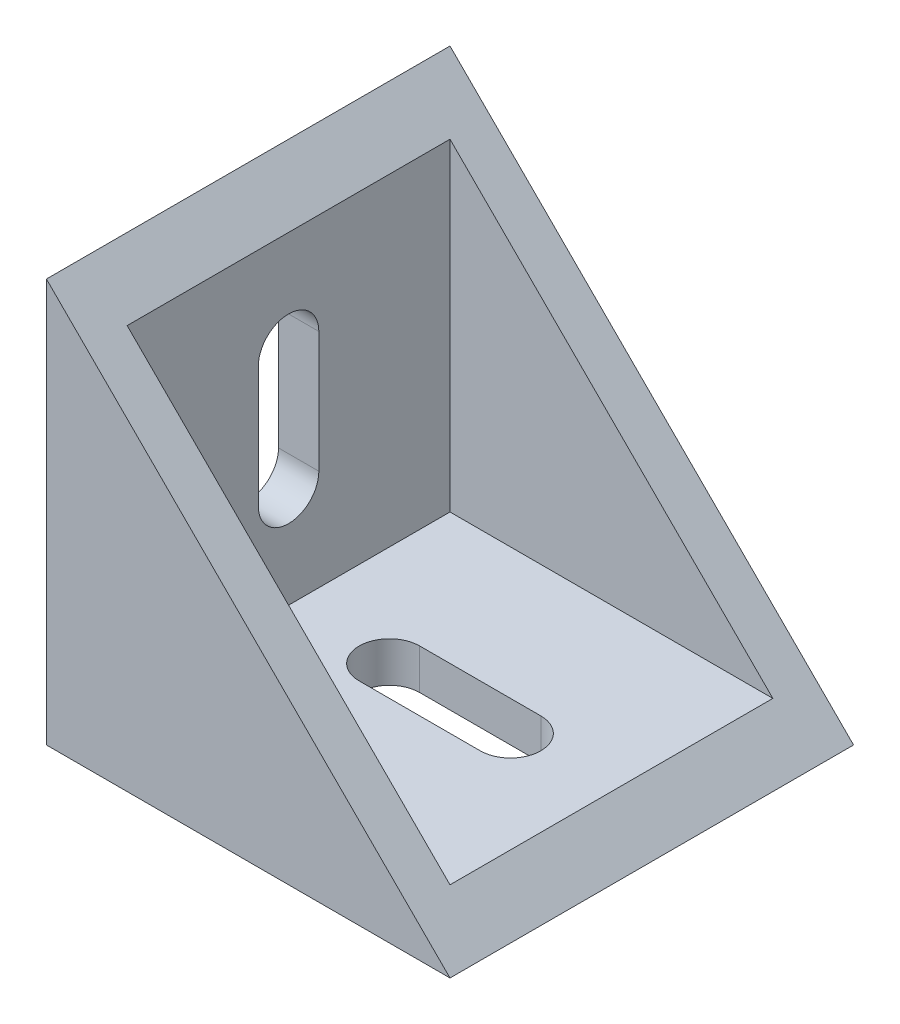
SolidWorks part; units mm, degrees
ref_plane "Front Plane" through (0, 0, 0) normal (0, 0, 1) x (1, 0, 0)
ref_plane "Top Plane" through (0, 0, 0) normal (0, 1, 0) x (1, 0, 0)
ref_plane "Right Plane" through (0, 0, 0) normal (1, 0, 0) x (0, 0, -1)
sketch "Sketch1" plane through (0, 0, 0) normal (0, 0, 1) x (1, 0, 0)
  line L0 (-10, 10) -> (10, -10)
  line L1 (-10, -10) -> (10, -10)
  line L2 (-10, -10) -> (-10, 10)
  line L5 (-10, -10) -> (0, 0) construction
  line L6 (-10, 10) -> (10, -10) construction
  point P0 (0, 0)
  dimension "D1" = 20
extrude "Boss-Extrude1" add sketch "Sketch1" along normal blind 20
shell "Shell1" thickness 2
sketch "Sketch2" plane through (-8, 0, 0) normal (1, 0, 0) x (0, 0, -1)
  line L3 (-11.5, 3) -> (-11.5, -3)
  line L4 (-8.5, 3) -> (-8.5, -3)
  arc A0 (-8.5, 3) -> (-11.5, 3) centre (-10, 3) ccw
  arc A1 (-11.5, -3) -> (-8.5, -3) centre (-10, -3) ccw
  dimension "D2" = 3
extrude "Cut-Extrude1" cut sketch "Sketch2" against normal blind 20
sketch "Sketch3" plane through (0, -8, 0) normal (0, 1, 0) x (1, 0, 0)
  line L3 (-3, -8.5) -> (3, -8.5)
  line L4 (-3, -11.5) -> (3, -11.5)
  arc A0 (-3, -8.5) -> (-3, -11.5) centre (-3, -10) ccw
  arc A1 (3, -11.5) -> (3, -8.5) centre (3, -10) ccw
  dimension "D1" = 3
extrude "Cut-Extrude2" cut sketch "Sketch3" against normal blind 20
